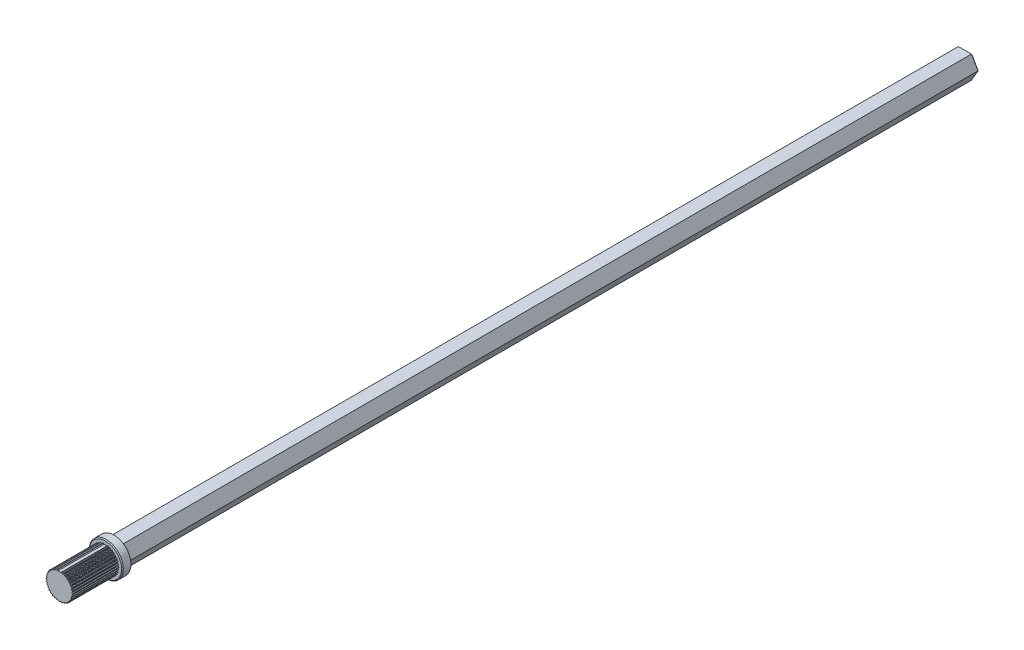
SolidWorks part; units mm, degrees
material "201 Annealed Stainless Steel (SS)"
ref_plane "Front Plane" through (0, 0, 0) normal (0, 0, 1) x (1, 0, 0)
ref_plane "Top Plane" through (0, 0, 0) normal (0, 1, 0) x (1, 0, 0)
ref_plane "Right Plane" through (0, 0, 0) normal (1, 0, 0) x (0, 0, -1)
sketch "Sketch1" plane through (0, 0, 0) normal (0, 0, 1) x (1, 0, 0)
  line L1 (7.6961, 0) -> (3.848, 6.665)
  line L2 (3.848, 6.665) -> (-3.848, 6.665)
  line L3 (-3.848, 6.665) -> (-7.6961, 0)
  line L4 (-7.6961, 0) -> (-3.848, -6.665)
  line L5 (-3.848, -6.665) -> (3.848, -6.665)
  line L6 (3.848, -6.665) -> (7.6961, 0)
  circle A0 centre (0, 0) radius 6.665 construction
  dimension "D1" = 13.33
extrude "Boss-Extrude1" add sketch "Sketch1" along normal blind 500
sketch "Sketch2" plane through (0, 0, 500) normal (0, 0, 1) x (1, 0, 0)
  circle A0 centre (0, 0) radius 10
  dimension "D1" = 20
extrude "Boss-Extrude2" add sketch "Sketch2" along normal blind 5
sketch "Sketch3" plane through (0, 0, 505) normal (0, 0, 1) x (1, 0, 0)
  line L0 (5.9329, 5.1084) -> (5.4037, 5.1084)
  line L1 (5.1084, 5.9329) -> (5.1084, 5.4037)
  line L2 (6.7298, 4.0006) -> (6.2087, 4.0925)
  line L3 (6.061, 4.9557) -> (5.9692, 4.4346)
  line L4 (7.6922, 1.4576) -> (7.234, 1.7221)
  line L5 (7.3904, 2.5838) -> (7.1259, 2.1256)
  line L6 (7.3222, 2.7712) -> (6.825, 2.9521)
  line L7 (6.8295, 3.8279) -> (6.6485, 3.3307)
  line L8 (7.8285, 0.0997) -> (7.4231, 0.4398)
  line L9 (7.7268, -1.2612) -> (7.3867, -0.8559)
  line L10 (7.8285, -0.0997) -> (7.4231, -0.4398)
  line L11 (6.8295, -3.8279) -> (6.6485, -3.3307)
  line L12 (6.7298, -4.0006) -> (6.2087, -4.0925)
  line L13 (7.3222, -2.7712) -> (6.825, -2.9521)
  line L14 (7.3904, -2.5838) -> (7.1259, -2.1256)
  line L15 (7.6922, -1.4576) -> (7.234, -1.7221)
  line L16 (6.061, -4.9557) -> (5.9692, -4.4346)
  line L17 (5.9329, -5.1084) -> (5.4037, -5.1084)
  line L18 (5.1084, -5.9329) -> (5.1084, -5.4037)
  line L19 (7.7268, 1.2612) -> (7.3867, 0.8559)
  line L20 (3.8279, 6.8295) -> (3.3307, 6.6485)
  line L21 (2.5838, 7.3904) -> (2.1256, 7.1259)
  line L22 (1.2612, 7.7268) -> (0.8559, 7.3867)
  line L23 (1.4576, 7.6922) -> (1.7221, 7.234)
  line L24 (2.7712, 7.3222) -> (2.9521, 6.825)
  line L25 (-1.2612, 7.7268) -> (-0.8559, 7.3867)
  line L26 (-2.5838, 7.3904) -> (-2.1256, 7.1259)
  line L27 (-2.7712, 7.3222) -> (-2.9521, 6.825)
  line L28 (-1.4576, 7.6922) -> (-1.7221, 7.234)
  line L29 (-0.8559, 7.3867) -> (0.8559, 7.3867)
  line L30 (4.9557, 6.061) -> (4.4346, 5.9692)
  line L31 (4.0006, 6.7298) -> (4.0925, 6.2087)
  line L32 (-5.9329, 5.1084) -> (-5.4037, 5.1084)
  line L33 (-5.1084, 5.9329) -> (-5.1084, 5.4037)
  line L34 (-4.9557, 6.061) -> (-4.4346, 5.9692)
  line L35 (-6.7298, 4.0006) -> (-6.2087, 4.0925)
  line L36 (-6.061, 4.9557) -> (-5.9692, 4.4346)
  line L37 (-7.3222, 2.7712) -> (-6.825, 2.9521)
  line L38 (-7.6922, 1.4576) -> (-7.234, 1.7221)
  line L39 (-7.3904, 2.5838) -> (-7.1259, 2.1256)
  line L40 (-6.8295, 3.8279) -> (-6.6485, 3.3307)
  line L41 (-4.0006, 6.7298) -> (-4.0925, 6.2087)
  line L42 (-3.8279, 6.8295) -> (-3.3307, 6.6485)
  line L43 (4.9557, -6.061) -> (4.4346, -5.9692)
  line L44 (2.5838, -7.3904) -> (2.1256, -7.1259)
  line L45 (1.2612, -7.7268) -> (0.8559, -7.3867)
  line L46 (1.4576, -7.6922) -> (1.7221, -7.234)
  line L47 (2.7712, -7.3222) -> (2.9521, -6.825)
  line L48 (4.0006, -6.7298) -> (4.0925, -6.2087)
  line L49 (3.8279, -6.8295) -> (3.3307, -6.6485)
  line L50 (0.0997, -7.8285) -> (0.4398, -7.4231)
  line L51 (-0.0997, -7.8285) -> (-0.4398, -7.4231)
  line L52 (-1.2612, -7.7268) -> (-0.8559, -7.3867)
  line L53 (-2.5838, -7.3904) -> (-2.1256, -7.1259)
  line L54 (-2.7712, -7.3222) -> (-2.9521, -6.825)
  line L55 (-1.4576, -7.6922) -> (-1.7221, -7.234)
  line L56 (-7.8285, 0.0997) -> (-7.4231, 0.4398)
  line L57 (-7.7268, -1.2612) -> (-7.3867, -0.8559)
  line L58 (-7.8285, -0.0997) -> (-7.4231, -0.4398)
  line L59 (-7.3904, -2.5838) -> (-7.1259, -2.1256)
  line L60 (-6.8295, -3.8279) -> (-6.6485, -3.3307)
  line L61 (-6.7298, -4.0006) -> (-6.2087, -4.0925)
  line L62 (-7.3222, -2.7712) -> (-6.825, -2.9521)
  line L63 (-7.6922, -1.4576) -> (-7.234, -1.7221)
  line L64 (-5.9329, -5.1084) -> (-5.4037, -5.1084)
  line L65 (-4.9557, -6.061) -> (-4.4346, -5.9692)
  line L66 (-5.1084, -5.9329) -> (-5.1084, -5.4037)
  line L67 (-6.061, -4.9557) -> (-5.9692, -4.4346)
  line L68 (-4.0006, -6.7298) -> (-4.0925, -6.2087)
  line L69 (-3.8279, -6.8295) -> (-3.3307, -6.6485)
  line L70 (4.0811, -6.273) -> (-4.0811, -6.273) construction
  line L71 (-7.7268, 1.2612) -> (-7.3867, 0.8559)
  arc A0 (5.4037, 5.1084) -> (5.1084, 5.4037) centre (0, 0) ccw
  arc A1 (6.8295, 3.8279) -> (6.7298, 4.0006) centre (6.7072, 3.8724) ccw
  arc A2 (6.2087, 4.0925) -> (5.9692, 4.4346) centre (0, 0) ccw
  arc A3 (6.061, 4.9557) -> (5.9329, 5.1084) centre (5.9329, 4.9783) ccw
  arc A4 (7.3904, 2.5838) -> (7.3222, 2.7712) centre (7.2777, 2.6489) ccw
  arc A5 (7.7268, 1.2612) -> (7.6922, 1.4576) centre (7.6271, 1.3449) ccw
  arc A6 (6.825, 2.9521) -> (6.6485, 3.3307) centre (0, 0) ccw
  arc A7 (7.234, 1.7221) -> (7.1259, 2.1256) centre (0, 0) ccw
  arc A8 (7.8285, -0.0997) -> (7.8285, 0.0997) centre (7.7448, 0) ccw
  arc A9 (7.4231, 0.4398) -> (7.3867, 0.8559) centre (0, 0) ccw
  arc A10 (7.3867, -0.8559) -> (7.4231, -0.4398) centre (0, 0) ccw
  arc A11 (7.6922, -1.4576) -> (7.7268, -1.2612) centre (7.6271, -1.3449) ccw
  arc A12 (7.3222, -2.7712) -> (7.3904, -2.5838) centre (7.2777, -2.6489) ccw
  arc A13 (7.1259, -2.1256) -> (7.234, -1.7221) centre (0, 0) ccw
  arc A14 (6.7298, -4.0006) -> (6.8295, -3.8279) centre (6.7072, -3.8724) ccw
  arc A15 (6.6485, -3.3307) -> (6.825, -2.9521) centre (0, 0) ccw
  arc A16 (5.1084, -5.4037) -> (5.4037, -5.1084) centre (0, 0) ccw
  arc A17 (5.9329, -5.1084) -> (6.061, -4.9557) centre (5.9329, -4.9783) ccw
  arc A18 (5.9692, -4.4346) -> (6.2087, -4.0925) centre (0, 0) ccw
  arc A19 (3.3307, 6.6485) -> (2.9521, 6.825) centre (0, 0) ccw
  arc A20 (4.0006, 6.7298) -> (3.8279, 6.8295) centre (3.8724, 6.7072) ccw
  arc A21 (1.4576, 7.6922) -> (1.2612, 7.7268) centre (1.3449, 7.6271) ccw
  arc A22 (2.7712, 7.3222) -> (2.5838, 7.3904) centre (2.6489, 7.2777) ccw
  arc A23 (2.1256, 7.1259) -> (1.7221, 7.234) centre (0, 0) ccw
  arc A24 (-1.2612, 7.7268) -> (-1.4576, 7.6922) centre (-1.3449, 7.6271) ccw
  arc A25 (-1.7221, 7.234) -> (-2.1256, 7.1259) centre (0, 0) ccw
  arc A26 (-2.9521, 6.825) -> (-3.3307, 6.6485) centre (0, 0) ccw
  arc A27 (-2.5838, 7.3904) -> (-2.7712, 7.3222) centre (-2.6489, 7.2777) ccw
  arc A28 (4.4346, 5.9692) -> (4.0925, 6.2087) centre (0, 0) ccw
  arc A29 (-3.8279, 6.8295) -> (-4.0006, 6.7298) centre (-3.8724, 6.7072) ccw
  arc A30 (-4.0925, 6.2087) -> (-4.4346, 5.9692) centre (0, 0) ccw
  arc A31 (-5.1084, 5.4037) -> (-5.4037, 5.1084) centre (0, 0) ccw
  arc A32 (-4.9557, 6.061) -> (-5.1084, 5.9329) centre (-4.9783, 5.9329) ccw
  arc A33 (-6.7298, 4.0006) -> (-6.8295, 3.8279) centre (-6.7072, 3.8724) ccw
  arc A34 (-5.9329, 5.1084) -> (-6.061, 4.9557) centre (-5.9329, 4.9783) ccw
  arc A35 (-5.9692, 4.4346) -> (-6.2087, 4.0925) centre (0, 0) ccw
  arc A36 (-6.6485, 3.3307) -> (-6.825, 2.9521) centre (0, 0) ccw
  arc A37 (-7.3222, 2.7712) -> (-7.3904, 2.5838) centre (-7.2777, 2.6489) ccw
  arc A38 (-7.1259, 2.1256) -> (-7.234, 1.7221) centre (0, 0) ccw
  arc A39 (-7.6922, 1.4576) -> (-7.7268, 1.2612) centre (-7.6271, 1.3449) ccw
  arc A41 (4.0925, -6.2087) -> (4.4346, -5.9692) centre (0, 0) ccw
  arc A42 (3.8279, -6.8295) -> (4.0006, -6.7298) centre (3.8724, -6.7072) ccw
  arc A43 (2.5838, -7.3904) -> (2.7712, -7.3222) centre (2.6489, -7.2777) ccw
  arc A44 (1.2612, -7.7268) -> (1.4576, -7.6922) centre (1.3449, -7.6271) ccw
  arc A45 (1.7221, -7.234) -> (2.1256, -7.1259) centre (0, 0) ccw
  arc A46 (2.9521, -6.825) -> (3.3307, -6.6485) centre (0, 0) ccw
  arc A47 (-0.0997, -7.8285) -> (0.0997, -7.8285) centre (0, -7.7448) ccw
  arc A48 (-1.4576, -7.6922) -> (-1.2612, -7.7268) centre (-1.3449, -7.6271) ccw
  arc A49 (-0.8559, -7.3867) -> (-0.4398, -7.4231) centre (0, 0) ccw
  arc A50 (-2.1256, -7.1259) -> (-1.7221, -7.234) centre (0, 0) ccw
  arc A51 (-2.7712, -7.3222) -> (-2.5838, -7.3904) centre (-2.6489, -7.2777) ccw
  arc A52 (-3.3307, -6.6485) -> (-2.9521, -6.825) centre (0, 0) ccw
  arc A53 (0.4398, -7.4231) -> (0.8559, -7.3867) centre (0, 0) ccw
  arc A54 (-7.8285, 0.0997) -> (-7.8285, -0.0997) centre (-7.7448, 0) ccw
  arc A55 (-7.3867, 0.8559) -> (-7.4231, 0.4398) centre (0, 0) ccw
  arc A56 (-7.4231, -0.4398) -> (-7.3867, -0.8559) centre (0, 0) ccw
  arc A57 (-7.7268, -1.2612) -> (-7.6922, -1.4576) centre (-7.6271, -1.3449) ccw
  arc A58 (-7.3904, -2.5838) -> (-7.3222, -2.7712) centre (-7.2777, -2.6489) ccw
  arc A59 (-7.234, -1.7221) -> (-7.1259, -2.1256) centre (0, 0) ccw
  arc A60 (-6.825, -2.9521) -> (-6.6485, -3.3307) centre (0, 0) ccw
  arc A61 (-6.8295, -3.8279) -> (-6.7298, -4.0006) centre (-6.7072, -3.8724) ccw
  arc A62 (-5.4037, -5.1084) -> (-5.1084, -5.4037) centre (0, 0) ccw
  arc A63 (-4.4346, -5.9692) -> (-4.0925, -6.2087) centre (0, 0) ccw
  arc A64 (-5.1084, -5.9329) -> (-4.9557, -6.061) centre (-4.9783, -5.9329) ccw
  arc A65 (-6.061, -4.9557) -> (-5.9329, -5.1084) centre (-5.9329, -4.9783) ccw
  arc A66 (-4.0006, -6.7298) -> (-3.8279, -6.8295) centre (-3.8724, -6.7072) ccw
  arc A67 (-6.2087, -4.0925) -> (-5.9692, -4.4346) centre (0, 0) ccw
  arc A68 (4.9557, -6.061) -> (5.1084, -5.9329) centre (4.9783, -5.9329) ccw
  arc A69 (5.1084, 5.9329) -> (4.9557, 6.061) centre (4.9783, 5.9329) ccw
extrude "Boss-Extrude3" add sketch "Sketch3" along normal blind 27
chamfer "Pah1" distance 0.5 angle 45 7 edges at (-5.7721, 3.3325, 0) (-5.7721, -3.3325, 0) (0, -6.665, 0) (5.7721, -3.3325, 0) (0, 6.665, 0) (5.7721, 3.3325, 0) (10, 0, 505)
